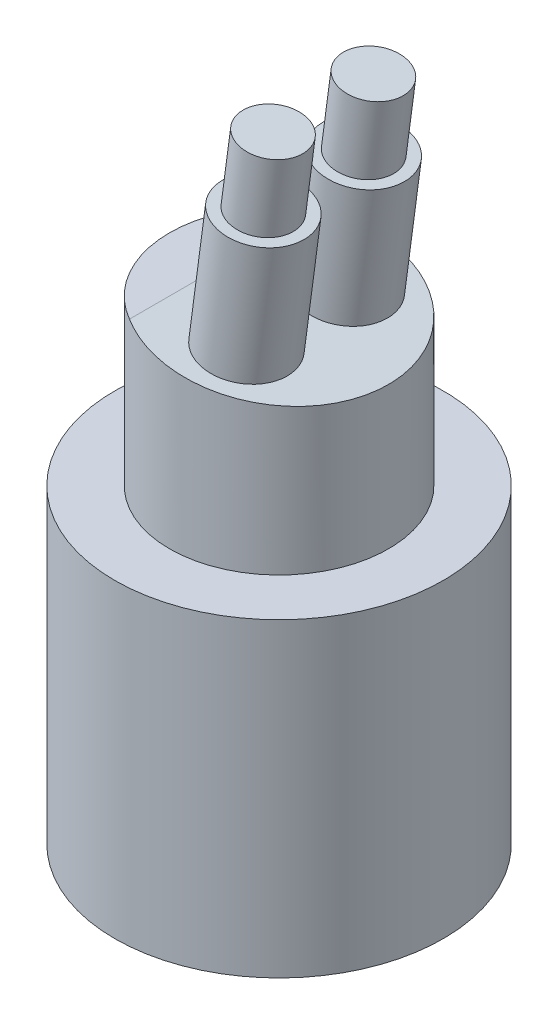
SolidWorks part; units mm, degrees
ref_plane "Front" through (0, 0, 0) normal (0, 0, 1) x (1, 0, 0)
ref_plane "Top" through (0, 0, 0) normal (0, 1, 0) x (1, 0, 0)
ref_plane "Right" through (0, 0, 0) normal (1, 0, 0) x (0, 0, -1)
sketch "Sketch1" plane through (0, 0, 0) normal (0, 1, 0) x (1, 0, 0)
  circle A0 centre (0, 0) radius 9
  dimension "D1" = 18
extrude "Boss-Extrude1" add sketch "Sketch1" along normal blind 17
sketch "Sketch2" plane through (0, 17, 0) normal (0, 1, 0) x (1, 0, 0)
  circle A0 centre (0, 0) radius 6
  dimension "D1" = 12
extrude "Boss-Extrude2" add sketch "Sketch2" along normal blind 9
sketch "Sketch3" plane through (0, 0, 0) normal (0, 0, 1) x (1, 0, 0)
  line L0 (-3, 26) -> (6, 26)
  line L2 (6, 26) -> (6, 24.8)
  line L4 (6, 24.8) -> (-3, 26)
  line L5 (6, 26) -> (-6, 26) construction
  line L6 (6, 17) -> (6, 26) construction
  dimension "D1" = 1.2
  dimension "D2" = 9
extrude "Cut-Extrude1" cut sketch "Sketch3" against normal mid plane 17
sketch "Sketch4" plane through (3.3537, 25.1528, 0) normal (0.1322, 0.9912, 0) x (0.9912, -0.1322, 0)
  line L0 (-6.4099, 5.1962) -> (-6.4099, -5.1962) construction
  circle A0 centre (-2.4099, 2.75) radius 2.25
  circle A1 centre (-2.4099, -2.75) radius 2.25
  dimension "D1" = 4.5
  dimension "D2" = 4.5
  dimension "D3" = 5.5
  dimension "D4" = 4
  dimension "D5" = 2.75
extrude "Boss-Extrude3" add sketch "Sketch4" along normal blind 11
sketch "Sketch5" plane through (4.8075, 36.0563, 0) normal (0.1322, 0.9912, 0) x (0.9912, -0.1322, 0)
  circle A2 centre (-2.4099, -2.75) radius 1.65
  circle A3 centre (-2.4099, -2.75) radius 1.65
  circle A4 centre (-2.4099, 2.75) radius 2.25 construction
  circle A5 centre (-2.4099, 2.75) radius 1.65
  circle A6 centre (-2.4099, 2.75) radius 1.65
  circle A7 centre (-2.4099, 2.75) radius 2.25
  circle A8 centre (-2.4099, -2.75) radius 2.25 construction
  circle A9 centre (-2.4099, -2.75) radius 2.25
  dimension "D1" = 0.6
  dimension "D2" = 0.6
extrude "Cut-Extrude2" cut sketch "Sketch5" against normal blind 4
sketch "Sketch6" plane through (0, 0, 0) normal (0, -1, 0) x (1, 0, 0)
  circle A0 centre (0, 0) radius 2.05
  dimension "D1" = 4.1
extrude "Cut-Extrude3" cut sketch "Sketch6" against normal blind 5
